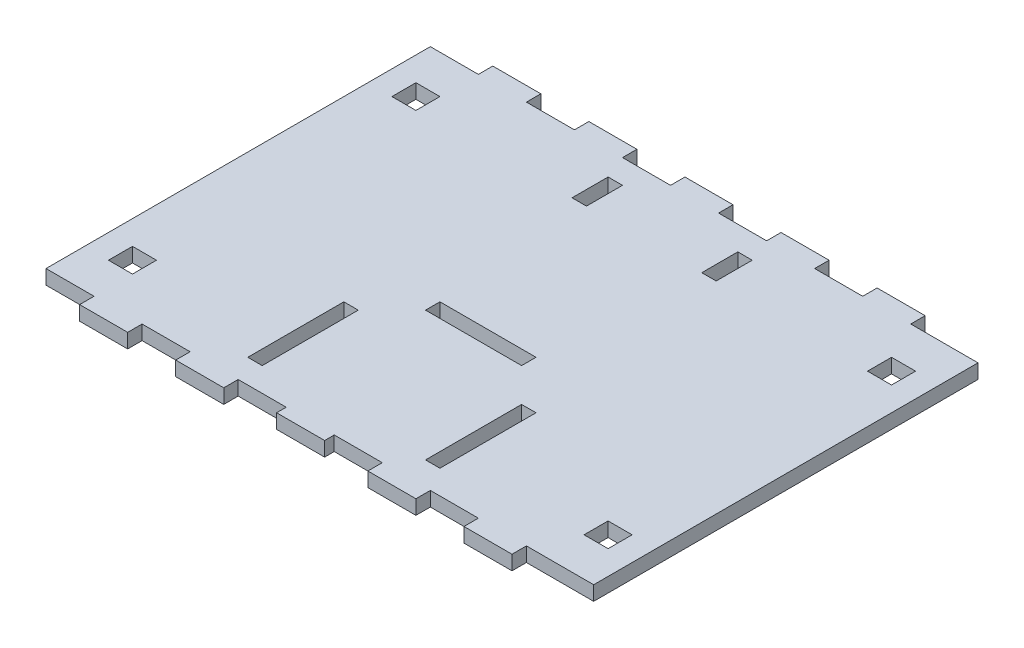
SolidWorks part; units mm, degrees
ref_plane "Front Plane" through (0, 0, 0) normal (0, 0, 1) x (1, 0, 0)
ref_plane "Top Plane" through (0, 0, 0) normal (0, 1, 0) x (1, 0, 0)
ref_plane "Right Plane" through (0, 0, 0) normal (1, 0, 0) x (0, 0, -1)
sketch "Sketch1" plane through (0, 0, 0) normal (0, 1, 0) x (1, 0, 0)
  line L0 (0, -191.0377) -> (0, 223.1132) construction
  line L1 (-94, 86) -> (-74, 86)
  line L2 (-114, 80) -> (-114, -80)
  line L3 (-114, -80) -> (-94, -80)
  line L4 (114, 80) -> (114, -80)
  line L5 (-308.4906, 0) -> (319.8113, 0) construction
  line L6 (-54, 86) -> (-34, 86)
  line L7 (-34, 86) -> (-34, 80)
  line L8 (-74, 86) -> (-74, 80)
  line L9 (-114, 80) -> (-94, 80)
  line L10 (-94, 86) -> (-94, 80)
  line L11 (-54, 86) -> (-54, 80)
  line L12 (-14, 86) -> (6, 86)
  line L13 (6, 86) -> (6, 80)
  line L14 (-14, 86) -> (-14, 80)
  line L15 (26, 86) -> (46, 86)
  line L16 (46, 86) -> (46, 80)
  line L17 (26, 86) -> (26, 80)
  line L18 (66, 86) -> (86, 86)
  line L19 (-74, 80) -> (-54, 80)
  line L20 (86, 86) -> (86, 80)
  line L21 (66, 86) -> (66, 80)
  line L22 (86, -80) -> (114, -80)
  line L23 (-34, 80) -> (-14, 80)
  line L24 (6, 80) -> (26, 80)
  line L25 (46, 80) -> (66, 80)
  line L26 (86, 80) -> (114, 80)
  line L27 (46, -86) -> (46, -80)
  line L28 (26, -86) -> (46, -86)
  line L29 (66, -86) -> (66, -80)
  line L30 (86, -86) -> (86, -80)
  line L31 (66, -86) -> (86, -86)
  line L32 (46, -80) -> (66, -80)
  line L33 (6, -80) -> (26, -80)
  line L34 (-34, -80) -> (-14, -80)
  line L35 (-74, -80) -> (-54, -80)
  line L36 (26, -86) -> (26, -80)
  line L37 (-14, -86) -> (-14, -80)
  line L38 (6, -86) -> (6, -80)
  line L39 (-14, -86) -> (6, -86)
  line L40 (-54, -86) -> (-54, -80)
  line L41 (-94, -86) -> (-94, -80)
  line L42 (-74, -86) -> (-74, -80)
  line L43 (-34, -86) -> (-34, -80)
  line L44 (-54, -86) -> (-34, -86)
  line L45 (-94, -86) -> (-74, -86)
  dimension "D3" = 20
  dimension "D4" = 6
  dimension "D1" = 228
  dimension "D6" = 114
  dimension "D7" = 28
  dimension "D2" = 172
  dimension "D5" = 5
extrude "Boss-Extrude1" add sketch "Sketch1" along normal blind 6
sketch "Sketch2" plane through (0, 0, 0) normal (0, 1, 0) x (1, 0, 0)
  line L0 (0, 165.1865) -> (0, -151.7884) construction
  line L1 (-104, 64) -> (-94, 64)
  line L2 (-104, 64) -> (-104, 54)
  line L3 (-104, 54) -> (-94, 54)
  line L4 (-94, 64) -> (-94, 54)
  line L5 (-158.5345, 0) -> (159.5055, 0) construction
  line L6 (-114, 80) -> (-114, -80) construction
  line L7 (-94, 80) -> (-114, 80) construction
  line L8 (104, 54) -> (94, 54)
  line L9 (104, 64) -> (104, 54)
  line L10 (94, 64) -> (94, 54)
  line L11 (104, 64) -> (94, 64)
  line L12 (104, -64) -> (94, -64)
  line L13 (94, -64) -> (94, -54)
  line L14 (104, -64) -> (104, -54)
  line L15 (104, -54) -> (94, -54)
  line L16 (-94, -64) -> (-94, -54)
  line L17 (-104, -54) -> (-94, -54)
  line L18 (-104, -64) -> (-104, -54)
  line L19 (-104, -64) -> (-94, -64)
  dimension "D1" = 10
  dimension "D2" = 10
  dimension "D3" = 16
extrude "Cut-Extrude1" cut sketch "Sketch2" along normal blind 6
sketch "Sketch4" plane through (0, 6, 0) normal (0, 1, 0) x (1, 0, 0)
  line L0 (0, 149.6913) -> (0, -216.5608) construction
  line L1 (-20, -10) -> (20, -10)
  line L2 (-20, -10) -> (-20, -16)
  line L3 (-20, -16) -> (20, -16)
  line L4 (20, -10) -> (20, -16)
  line L5 (-20, -84) -> (20, -84)
  line L6 (-20, -84) -> (-20, -90)
  line L7 (-20, -90) -> (20, -90)
  line L8 (20, -84) -> (20, -90)
  line L9 (-40, -30) -> (-34, -30)
  line L10 (-40, -30) -> (-40, -70)
  line L11 (-40, -70) -> (-34, -70)
  line L12 (-34, -30) -> (-34, -70)
  line L13 (34, -30) -> (34, -70)
  line L14 (40, -70) -> (34, -70)
  line L15 (40, -30) -> (40, -70)
  line L16 (40, -30) -> (34, -30)
  line L17 (-14, 80) -> (-34, 80) construction
  line L18 (-30, 70) -> (-24, 70)
  line L19 (-30, 70) -> (-30, 55)
  line L20 (-30, 55) -> (-24, 55)
  line L21 (-24, 70) -> (-24, 55)
  line L22 (24, 70) -> (24, 55)
  line L23 (30, 55) -> (24, 55)
  line L24 (30, 70) -> (30, 55)
  line L25 (30, 70) -> (24, 70)
  point P15 (0, -84)
  point P16 (0, -16)
  point P17 (-34, -50)
  dimension "D1" = 40
  dimension "D2" = 6
  dimension "D3" = 10
  dimension "D4" = 80
  dimension "D5" = 40
  dimension "D6" = 40
  dimension "D7" = 30
  dimension "D8" = 15
  dimension "D9" = 6
  dimension "D10" = 10
extrude "Cut-Extrude2" cut sketch "Sketch4" against normal blind 6
equation "\"Material Thickness\"= 6mm"
equation "\"D4@Sketch1\"=\"Material Thickness\""
equation "\"D1@Boss-Extrude1\"=\"Material Thickness\""
equation "\"D1@Cut-Extrude1\"=\"Material Thickness\""
equation "\"D2@Sketch4\"=\"Material Thickness\""
equation "\"D1@Cut-Extrude2\"=\"Material Thickness\""
equation "\"D9@Sketch4\"=\"Material Thickness\""
equation "\"D1@Sketch1\"=250-(\"Material Thickness\"*2)-10"
equation "\"D2@Sketch1\"=160+(\"Material Thickness\"*2)"
